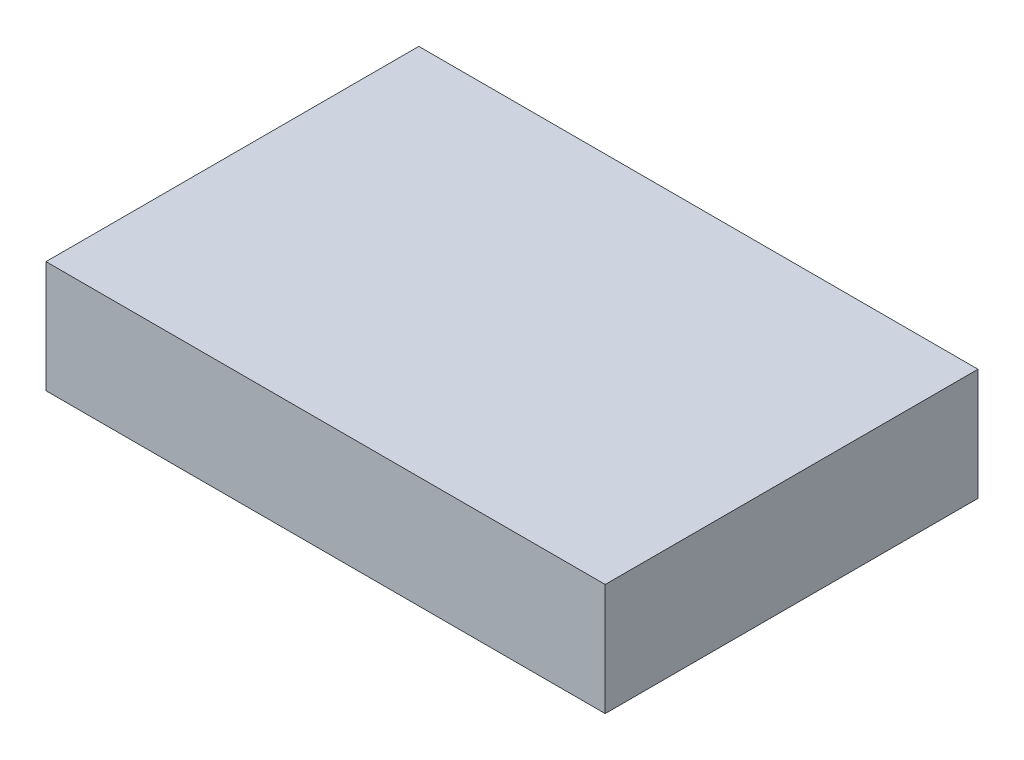
SolidWorks part; units mm, degrees
ref_plane "Přední rovina" through (0, 0, 0) normal (0, 0, 1) x (1, 0, 0)
ref_plane "Horní rovina" through (0, 0, 0) normal (0, 1, 0) x (1, 0, 0)
ref_plane "Pravá rovina" through (0, 0, 0) normal (1, 0, 0) x (0, 0, -1)
sketch "Sketch1" plane through (0, 0, 0) normal (0, 1, 0) x (1, 0, 0)
  line L1 (-75, 50) -> (75, 50)
  line L2 (-75, 50) -> (-75, -50)
  line L3 (-75, -50) -> (75, -50)
  line L4 (75, 50) -> (75, -50)
  line L5 (-75, 50) -> (75, -50) construction
  line L6 (-75, -50) -> (75, 50) construction
  point P0 (0, 0)
  dimension "D1" = 100
  dimension "D2" = 150
extrude "Extrude1" add sketch "Sketch1" along normal blind 30
